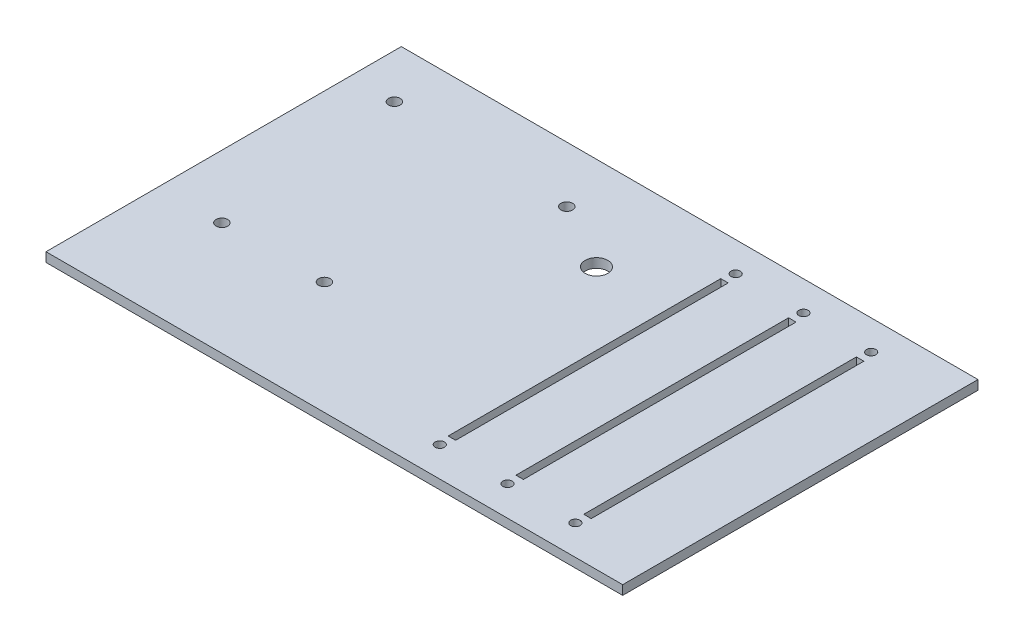
SolidWorks part; units mm, degrees
ref_plane "Front Plane" through (0, 0, 0) normal (0, 0, 1) x (1, 0, 0)
ref_plane "Top Plane" through (0, 0, 0) normal (0, 1, 0) x (1, 0, 0)
ref_plane "Right Plane" through (0, 0, 0) normal (1, 0, 0) x (0, 0, -1)
sketch "Sketch1" plane through (0, 0, 0) normal (0, 1, 0) x (1, 0, 0)
  line L0 (-69.0563, 48.4187) -> (-69.0563, -48.4187) construction
  line L1 (-78.5813, -48.4187) -> (78.5812, -48.4187)
  line L2 (-78.5813, -48.4187) -> (-78.5813, 48.4187)
  line L3 (-78.5813, 48.4187) -> (78.5812, 48.4187)
  line L4 (78.5812, -48.4187) -> (78.5812, 48.4187)
  line L5 (-78.5813, -48.4187) -> (78.5812, 48.4187) construction
  line L6 (-78.5813, 48.4187) -> (78.5812, -48.4187) construction
  line L7 (69.0562, 48.4187) -> (69.0562, -48.4187) construction
  line L8 (-78.5813, 38.8937) -> (78.5812, 38.8937) construction
  line L9 (-78.5813, -38.8937) -> (78.5812, -38.8937) construction
  line L10 (-69.0563, -20.1613) -> (-15.7163, -20.1613) construction
  line L11 (-15.7163, -20.1613) -> (-15.7163, 48.4187) construction
  line L12 (-66.5163, 48.4187) -> (-66.5162, -20.1613) construction
  line L13 (-66.5163, 34.4487) -> (-15.7163, 34.4487) construction
  line L14 (-15.7163, 33.1787) -> (-66.5163, 33.1787) construction
  line L15 (-61.4363, 38.8937) -> (-61.4363, -20.1613) construction
  line L16 (-69.0563, -17.6213) -> (-15.7163, -17.6213) construction
  line L17 (-18.2563, 38.8937) -> (-18.2563, -17.6213) construction
  line L18 (50.5777, 44.1642) -> (64.8017, 44.1642) construction
  line L19 (64.8017, 44.1642) -> (64.8017, -44.1007) construction
  line L20 (64.8017, -44.1007) -> (50.5777, -44.1007) construction
  line L21 (50.5777, -44.1007) -> (50.5777, 44.1642) construction
  line L22 (32.0992, 44.1642) -> (46.3232, 44.1642) construction
  line L23 (46.3232, 44.1642) -> (46.3232, -44.1007) construction
  line L24 (46.3232, -44.1007) -> (32.0992, -44.1007) construction
  line L25 (32.0992, -44.1007) -> (32.0992, 44.1642) construction
  line L26 (13.6207, 44.1642) -> (27.8447, 44.1642) construction
  line L27 (27.8447, 44.1642) -> (27.8447, -44.1007) construction
  line L28 (27.8447, -44.1007) -> (13.6207, -44.1007) construction
  line L29 (13.6207, -44.1007) -> (13.6207, 44.1642) construction
  line L30 (21.7487, 37.1792) -> (21.7487, -37.1157)
  line L31 (21.7487, -37.1157) -> (19.7167, -37.1157)
  line L32 (19.7167, -37.1157) -> (19.7167, 37.1792)
  line L33 (19.7167, 37.1792) -> (21.7487, 37.1792)
  line L34 (40.2272, 37.1792) -> (40.2272, -37.1157)
  line L35 (40.2272, -37.1157) -> (38.1952, -37.1157)
  line L36 (38.1952, -37.1157) -> (38.1952, 37.1792)
  line L37 (38.1952, 37.1792) -> (40.2272, 37.1792)
  line L38 (58.7057, 37.1792) -> (58.7057, -37.1158)
  line L39 (58.7057, -37.1158) -> (56.6737, -37.1158)
  line L40 (56.6737, -37.1158) -> (56.6737, 37.1792)
  line L41 (56.6737, 37.1792) -> (58.7057, 37.1792)
  circle A0 centre (-66.5163, 34.4487) radius 1.5875
  circle A1 centre (-61.4363, -17.6213) radius 1.5875
  circle A2 centre (-33.4963, -17.6213) radius 1.5875
  circle A3 centre (-18.2563, 33.1787) radius 1.5875
  circle A4 centre (57.5627, 40.3288) radius 1.27
  circle A5 centre (39.0842, 40.3542) radius 1.27
  circle A6 centre (20.6057, 40.3542) radius 1.27
  circle A7 centre (57.5627, -40.2908) radius 1.27
  circle A8 centre (39.0842, -40.2907) radius 1.27
  circle A9 centre (20.6057, -40.2907) radius 1.27
  circle A10 centre (0, 23.0187) radius 3.0861
  point P0 (0, 0)
  point P28 (-61.4363, -17.6213)
  point P29 (-61.4363, -17.6213)
  point P36 (-18.2563, 33.1787)
  dimension "D11" = 3.175
  dimension "D15" = 3.175
  dimension "D16" = 3.175
  dimension "D19" = 3.175
  dimension "D44" = 2.54
  dimension "D51" = 2.54
  dimension "D52" = 2.54
  dimension "D59" = 2.54
  dimension "D60" = 2.54
  dimension "D61" = 2.54
  dimension "D62" = 6.1722
  dimension "D1" = 96.8375
  dimension "D2" = 157.1625
  dimension "D3" = 9.525
  dimension "D4" = 9.525
  dimension "D5" = 9.525
  dimension "D6" = 9.525
  dimension "D7" = 53.34
  dimension "D8" = 68.58
  dimension "D9" = 2.54
  dimension "D10" = 13.97
  dimension "D12" = 1.27
  dimension "D13" = 5.08
  dimension "D14" = 50.8
  dimension "D17" = 27.94
  dimension "D18" = 15.24
  dimension "D20" = 88.265
  dimension "D21" = 14.224
  dimension "D22" = 4.2545
  dimension "D23" = 4.2545
  dimension "D24" = 88.265
  dimension "D25" = 14.224
  dimension "D26" = 4.2545
  dimension "D27" = 4.2545
  dimension "D28" = 88.265
  dimension "D29" = 14.224
  dimension "D30" = 4.2545
  dimension "D31" = 4.2545
  dimension "D32" = 6.096
  dimension "D33" = 6.096
  dimension "D34" = 6.985
  dimension "D35" = 6.985
  dimension "D36" = 6.096
  dimension "D37" = 6.096
  dimension "D38" = 6.985
  dimension "D39" = 6.985
  dimension "D40" = 6.985
  dimension "D41" = 6.096
  dimension "D42" = 6.096
  dimension "D43" = 6.985
  dimension "D45" = 6.985
  dimension "D46" = 3.8354
  dimension "D47" = 6.985
  dimension "D48" = 6.985
  dimension "D49" = 3.81
  dimension "D50" = 3.81
  dimension "D53" = 6.985
  dimension "D54" = 6.985
  dimension "D55" = 6.985
  dimension "D56" = 3.81
  dimension "D57" = 3.81
  dimension "D58" = 3.81
  dimension "D63" = 25.4
extrude "Boss-Extrude1" add sketch "Sketch1" along normal blind 2.54 contours L3 L4 L1 L2
